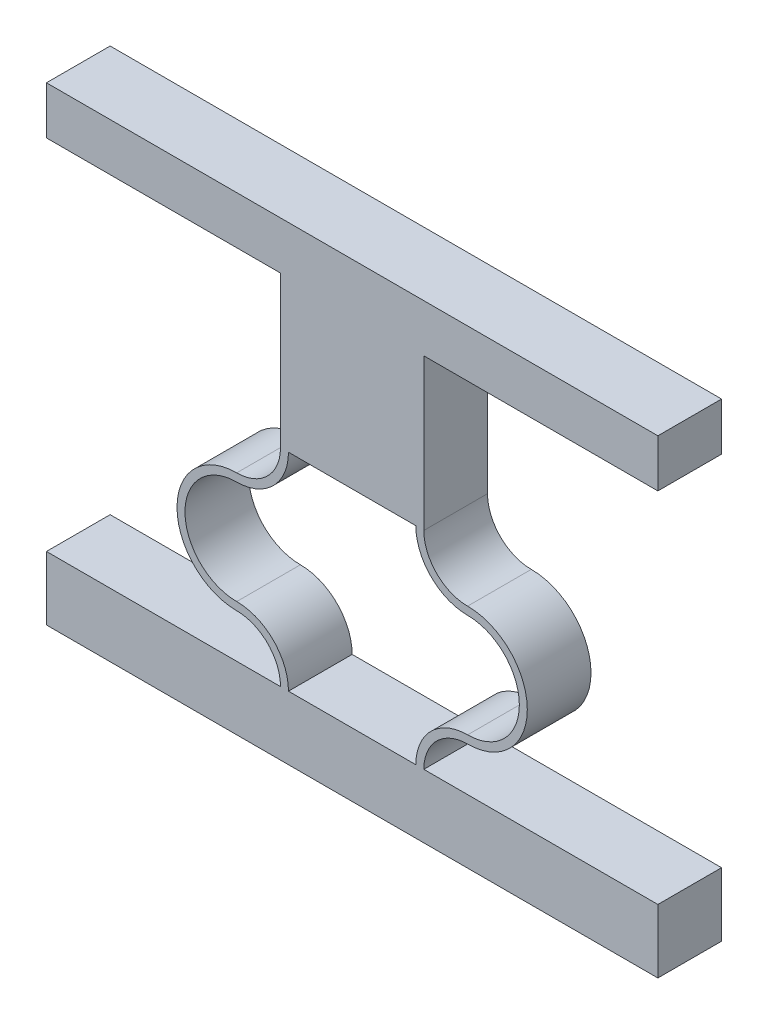
SolidWorks part; units mm, degrees
ref_plane "Front Plane" through (0, 0, 0) normal (0, 0, 1) x (1, 0, 0)
ref_plane "Top Plane" through (0, 0, 0) normal (0, 1, 0) x (1, 0, 0)
ref_plane "Right Plane" through (0, 0, 0) normal (1, 0, 0) x (0, 0, -1)
sketch "Sketch1" plane through (0, 0, 0) normal (0, 0, 1) x (1, 0, 0)
  line L4 (0, 11.5) -> (0, 0)
  line L5 (10.2, 0) -> (10.2, 13) construction
  line L6 (10.2, 13) -> (10.2, 15.9911) construction
  line L17 (9.7, 0) -> (0, 0)
  line L18 (10.7, 0) -> (20.4, 0)
  line L19 (20.4, 0) -> (20.4, 11.5)
  line L20 (10.7, 13.2411) -> (10.7, 14.4911)
  line L21 (9.7, 13.2411) -> (9.7, 14.4911)
  line L22 (10.7, 14.7411) -> (10.7, 15.9911)
  line L23 (10.7, 15.9911) -> (9.7, 15.9911)
  line L24 (9.7, 15.9911) -> (9.7, 14.7411)
  line L31 (-5, 13.25) -> (-5, -4)
  line L32 (-5, -4) -> (25.4, -4)
  line L33 (25.4, -4) -> (25.4, 13.25)
  line L34 (0, 11.75) -> (0, 13)
  line L36 (-5, 13.25) -> (0, 13.25)
  line L37 (25.4, 13.25) -> (20.4, 13.25)
  line L38 (20.4, 11.75) -> (20.4, 13)
  arc A0 (10.2, 13) -> (6.95, 9.75) centre (6.95, 13) cw
  arc A1 (6.95, 9.75) -> (6.95, 3.25) centre (6.95, 6.5) ccw
  arc A2 (6.95, 3.25) -> (10.2, 0) centre (6.95, 0) cw
  arc A3 (9.7, 12.9911) -> (6.95, 10.25) centre (6.95, 13) cw
  arc A4 (6.95, 10.25) -> (6.95, 2.75) centre (6.95, 6.5) ccw
  arc A5 (6.95, 2.75) -> (9.7, 0) centre (6.95, 0) cw
  arc A6 (9.7, 13) -> (6.95, 10.25) centre (6.95, 13) cw construction
  arc A7 (13.45, 3.25) -> (10.2, 0) centre (13.45, 0) ccw
  arc A8 (13.45, 2.75) -> (10.7, 0) centre (13.45, 0) ccw
  arc A9 (13.45, 9.75) -> (13.45, 3.25) centre (13.45, 6.5) cw
  arc A10 (13.45, 10.25) -> (13.45, 2.75) centre (13.45, 6.5) cw
  arc A11 (10.7, 12.9911) -> (13.45, 10.25) centre (13.45, 13) ccw
  arc A12 (10.2, 13) -> (13.45, 9.75) centre (13.45, 13) ccw
  spline S0 degree 4 poles (-2.0401, 11.8932) (-1.9772, 11.8846) (-1.8455, 11.8679) (-1.6624, 11.8447) (-1.3945, 11.8179) (-1.0936, 11.7897) (-0.7437, 11.7688) (-0.4752, 11.7554) (-0.0408, 11.749) (0.1102, 11.7499) (0.4738, 11.7558) (0.7092, 11.7679) (1.0334, 11.7851) (1.3516, 11.8128) (1.7502, 11.854) (2.1923, 11.9124) (2.7058, 11.9922) (3.3058, 12.1029) (4.0022, 12.2485) (4.9166, 12.4561) (5.9838, 12.707) (7.055, 12.9379) (8.1373, 13.1142) (9.0337, 13.2105) (9.8109, 13.2536) (10.5891, 13.2536) (11.3663, 13.2105) (12.2627, 13.1142) (13.3449, 12.9379) (14.4163, 12.707) (15.4832, 12.4561) (16.3198, 12.2662) (16.8578, 12.1523) (17.3629, 12.0533) (17.7764, 11.9798) (18.2035, 11.9124) (18.6563, 11.854) (18.9878, 11.8179) (19.2899, 11.793) (19.5137, 11.7765) (19.7423, 11.7659) (19.9174, 11.7558) (20.2941, 11.7499) (20.4363, 11.749) (20.8074, 11.7542) (21.0192, 11.7634) (21.2671, 11.7754) (21.4449, 11.7884) (21.6432, 11.8037) (21.8311, 11.8212) (22.0262, 11.8414) (22.2161, 11.864) (22.3445, 11.8804) (22.4082, 11.8889) (22.4399, 11.8932) knots 0 0 0 0 0 0.010394 0.020788 0.031182 0.041576 0.062112 0.07238 0.082649 0.098356 0.106209 0.114063 0.12977 0.145477 0.161184 0.176891 0.202819 0.228747 0.260161 0.291575 0.354403 0.405758 0.437172 0.468586 0.5 0.531414 0.562828 0.594242 0.645597 0.708425 0.739839 0.771253 0.784217 0.797181 0.823109 0.838816 0.854523 0.87023 0.878084 0.885937 0.893791 0.901644 0.917351 0.92762 0.937888 0.948156 0.958424 0.963621 0.968818 0.979212 0.989606 0.994803 1 1 1 1 1 construction
  spline S1 degree 4 poles (0, 11.75) (0.0812, 11.75) (0.1997, 11.7513) (0.4738, 11.7558) (0.7092, 11.7679) (1.0334, 11.7851) (1.3516, 11.8128) (1.7502, 11.854) (2.1923, 11.9124) (2.7058, 11.9922) (3.3058, 12.1029) (4.0022, 12.2485) (4.9166, 12.4561) (5.9838, 12.707) (7.055, 12.9379) (8.1373, 13.1142) (9.0337, 13.2105) (9.8109, 13.2536) (10.5891, 13.2536) (11.3663, 13.2105) (12.2627, 13.1142) (13.3449, 12.9379) (14.4163, 12.707) (15.4832, 12.4561) (16.3198, 12.2662) (16.8578, 12.1523) (17.3629, 12.0533) (17.7764, 11.9798) (18.2035, 11.9124) (18.6563, 11.854) (18.9878, 11.8179) (19.2899, 11.793) (19.5137, 11.7765) (19.7423, 11.7659) (19.9174, 11.7558) (20.2013, 11.7513) (20.3188, 11.75) (20.4, 11.75) knots 0.082649 0.082649 0.082649 0.082649 0.082649 0.098356 0.106209 0.114063 0.12977 0.145477 0.161184 0.176891 0.202819 0.228747 0.260161 0.291575 0.354403 0.405758 0.437172 0.468586 0.5 0.531414 0.562828 0.594242 0.645597 0.708425 0.739839 0.771253 0.784217 0.797181 0.823109 0.838816 0.854523 0.87023 0.878084 0.885937 0.893791 0.901644 0.917351 0.917351 0.917351 0.917351 0.917351
  spline S2 degree 4 poles (-2.0401, 13.1432) (-1.9772, 13.1346) (-1.8455, 13.1179) (-1.6624, 13.0947) (-1.3945, 13.0679) (-1.0936, 13.0397) (-0.7437, 13.0188) (-0.4752, 13.0054) (-0.0408, 12.999) (0.1102, 12.9999) (0.4738, 13.0058) (0.7092, 13.0179) (1.0334, 13.0351) (1.3516, 13.0628) (1.7502, 13.104) (2.1923, 13.1624) (2.7058, 13.2422) (3.3058, 13.3529) (4.0022, 13.4985) (4.9166, 13.7061) (5.9838, 13.957) (7.055, 14.1879) (8.1373, 14.3642) (9.0337, 14.4605) (9.8109, 14.5036) (10.5891, 14.5036) (11.3663, 14.4605) (12.2627, 14.3642) (13.3449, 14.1879) (14.4163, 13.957) (15.4832, 13.7061) (16.3198, 13.5162) (16.8578, 13.4023) (17.3629, 13.3033) (17.7764, 13.2298) (18.2035, 13.1624) (18.6563, 13.104) (18.9878, 13.0679) (19.2899, 13.043) (19.5137, 13.0265) (19.7423, 13.0159) (19.9174, 13.0058) (20.2941, 12.9999) (20.4363, 12.999) (20.8074, 13.0042) (21.0192, 13.0134) (21.2671, 13.0254) (21.4449, 13.0384) (21.6432, 13.0537) (21.8311, 13.0712) (22.0262, 13.0914) (22.2161, 13.114) (22.3445, 13.1304) (22.4082, 13.1389) (22.4399, 13.1432) knots 0 0 0 0 0 0.010394 0.020788 0.031182 0.041576 0.062112 0.07238 0.082649 0.098356 0.106209 0.114063 0.12977 0.145477 0.161184 0.176891 0.202819 0.228747 0.260161 0.291575 0.354403 0.405758 0.437172 0.468586 0.5 0.531414 0.562828 0.594242 0.645597 0.708425 0.739839 0.771253 0.784217 0.797181 0.823109 0.838816 0.854523 0.87023 0.878084 0.885937 0.893791 0.901644 0.917351 0.92762 0.937888 0.948156 0.958424 0.963621 0.968818 0.979212 0.989606 0.994803 1 1 1 1 1 construction
  spline S3 degree 4 poles (0, 13) (0.0812, 13) (0.1997, 13.0013) (0.4738, 13.0058) (0.7092, 13.0179) (1.0334, 13.0351) (1.3516, 13.0628) (1.7502, 13.104) (2.1923, 13.1624) (2.7058, 13.2422) (3.3058, 13.3529) (4.0022, 13.4985) (4.9166, 13.7061) (5.9838, 13.957) (7.055, 14.1879) (8.1373, 14.3642) (9.0337, 14.4605) (9.8109, 14.5036) (10.5891, 14.5036) (11.3663, 14.4605) (12.2627, 14.3642) (13.3449, 14.1879) (14.4163, 13.957) (15.4832, 13.7061) (16.3198, 13.5162) (16.8578, 13.4023) (17.3629, 13.3033) (17.7764, 13.2298) (18.2035, 13.1624) (18.6563, 13.104) (18.9878, 13.0679) (19.2899, 13.043) (19.5137, 13.0265) (19.7423, 13.0159) (19.9174, 13.0058) (20.2013, 13.0013) (20.3188, 13) (20.4, 13) knots 0.082649 0.082649 0.082649 0.082649 0.082649 0.098356 0.106209 0.114063 0.12977 0.145477 0.161184 0.176891 0.202819 0.228747 0.260161 0.291575 0.354403 0.405758 0.437172 0.468586 0.5 0.531414 0.562828 0.594242 0.645597 0.708425 0.739839 0.771253 0.784217 0.797181 0.823109 0.838816 0.854523 0.87023 0.878084 0.885937 0.893791 0.901644 0.917351 0.917351 0.917351 0.917351 0.917351
  spline S4 degree 4 poles (-2.0401, 13.3932) (-1.9772, 13.3846) (-1.8455, 13.3679) (-1.6624, 13.3447) (-1.3945, 13.3179) (-1.0936, 13.2897) (-0.7437, 13.2688) (-0.4752, 13.2554) (-0.0408, 13.249) (0.1102, 13.2499) (0.4738, 13.2558) (0.7092, 13.2679) (1.0334, 13.2851) (1.3516, 13.3128) (1.7502, 13.354) (2.1923, 13.4124) (2.7058, 13.4922) (3.3058, 13.6029) (4.0022, 13.7485) (4.9166, 13.9561) (5.9838, 14.207) (7.055, 14.4379) (8.1373, 14.6142) (9.0337, 14.7105) (9.8109, 14.7536) (10.5891, 14.7536) (11.3663, 14.7105) (12.2627, 14.6142) (13.3449, 14.4379) (14.4163, 14.207) (15.4832, 13.9561) (16.3198, 13.7662) (16.8578, 13.6523) (17.3629, 13.5533) (17.7764, 13.4798) (18.2035, 13.4124) (18.6563, 13.354) (18.9878, 13.3179) (19.2899, 13.293) (19.5137, 13.2765) (19.7423, 13.2659) (19.9174, 13.2558) (20.2941, 13.2499) (20.4363, 13.249) (20.8074, 13.2542) (21.0192, 13.2634) (21.2671, 13.2754) (21.4449, 13.2884) (21.6432, 13.3037) (21.8311, 13.3212) (22.0262, 13.3414) (22.2161, 13.364) (22.3445, 13.3804) (22.4082, 13.3889) (22.4399, 13.3932) knots 0 0 0 0 0 0.010394 0.020788 0.031182 0.041576 0.062112 0.07238 0.082649 0.098356 0.106209 0.114063 0.12977 0.145477 0.161184 0.176891 0.202819 0.228747 0.260161 0.291575 0.354403 0.405758 0.437172 0.468586 0.5 0.531414 0.562828 0.594242 0.645597 0.708425 0.739839 0.771253 0.784217 0.797181 0.823109 0.838816 0.854523 0.87023 0.878084 0.885937 0.893791 0.901644 0.917351 0.92762 0.937888 0.948156 0.958424 0.963621 0.968818 0.979212 0.989606 0.994803 1 1 1 1 1 construction
  spline S5 degree 4 poles (0, 13.25) (0.0812, 13.25) (0.1997, 13.2513) (0.4738, 13.2558) (0.7092, 13.2679) (1.0334, 13.2851) (1.3516, 13.3128) (1.7502, 13.354) (2.1923, 13.4124) (2.7058, 13.4922) (3.3058, 13.6029) (4.0022, 13.7485) (4.9166, 13.9561) (5.9838, 14.207) (7.055, 14.4379) (8.1373, 14.6142) (9.0337, 14.7105) (9.8109, 14.7536) (10.5891, 14.7536) (11.3663, 14.7105) (12.2627, 14.6142) (13.3449, 14.4379) (14.4163, 14.207) (15.4832, 13.9561) (16.3198, 13.7662) (16.8578, 13.6523) (17.3629, 13.5533) (17.7764, 13.4798) (18.2035, 13.4124) (18.6563, 13.354) (18.9878, 13.3179) (19.2899, 13.293) (19.5137, 13.2765) (19.7423, 13.2659) (19.9174, 13.2558) (20.2013, 13.2513) (20.3188, 13.25) (20.4, 13.25) knots 0.082649 0.082649 0.082649 0.082649 0.082649 0.098356 0.106209 0.114063 0.12977 0.145477 0.161184 0.176891 0.202819 0.228747 0.260161 0.291575 0.354403 0.405758 0.437172 0.468586 0.5 0.531414 0.562828 0.594242 0.645597 0.708425 0.739839 0.771253 0.784217 0.797181 0.823109 0.838816 0.854523 0.87023 0.878084 0.885937 0.893791 0.901644 0.917351 0.917351 0.917351 0.917351 0.917351
  spline S8 degree 4 poles (-2.0401, 11.6432) (-1.9772, 11.6346) (-1.8455, 11.6179) (-1.6624, 11.5947) (-1.3945, 11.5679) (-1.0936, 11.5397) (-0.7437, 11.5188) (-0.4752, 11.5054) (-0.0408, 11.499) (0.1102, 11.4999) (0.4738, 11.5058) (0.7092, 11.5179) (1.0334, 11.5351) (1.3516, 11.5628) (1.7502, 11.604) (2.1923, 11.6624) (2.7058, 11.7422) (3.3058, 11.8529) (4.0022, 11.9985) (4.9166, 12.2061) (5.9838, 12.457) (7.055, 12.6879) (8.1373, 12.8642) (9.0337, 12.9605) (9.8109, 13.0036) (10.5891, 13.0036) (11.3663, 12.9605) (12.2627, 12.8642) (13.3449, 12.6879) (14.4163, 12.457) (15.4832, 12.2061) (16.3198, 12.0162) (16.8578, 11.9023) (17.3629, 11.8033) (17.7764, 11.7298) (18.2035, 11.6624) (18.6563, 11.604) (18.9878, 11.5679) (19.2899, 11.543) (19.5137, 11.5265) (19.7423, 11.5159) (19.9174, 11.5058) (20.2941, 11.4999) (20.4363, 11.499) (20.8074, 11.5042) (21.0192, 11.5134) (21.2671, 11.5254) (21.4449, 11.5384) (21.6432, 11.5537) (21.8311, 11.5712) (22.0262, 11.5914) (22.2161, 11.614) (22.3445, 11.6304) (22.4082, 11.6389) (22.4399, 11.6432) knots 0 0 0 0 0 0.010394 0.020788 0.031182 0.041576 0.062112 0.07238 0.082649 0.098356 0.106209 0.114063 0.12977 0.145477 0.161184 0.176891 0.202819 0.228747 0.260161 0.291575 0.354403 0.405758 0.437172 0.468586 0.5 0.531414 0.562828 0.594242 0.645597 0.708425 0.739839 0.771253 0.784217 0.797181 0.823109 0.838816 0.854523 0.87023 0.878084 0.885937 0.893791 0.901644 0.917351 0.92762 0.937888 0.948156 0.958424 0.963621 0.968818 0.979212 0.989606 0.994803 1 1 1 1 1 construction
  spline S9 degree 4 poles (0, 11.5) (0.0812, 11.5) (0.1997, 11.5013) (0.4738, 11.5058) (0.7092, 11.5179) (1.0334, 11.5351) (1.3516, 11.5628) (1.7502, 11.604) (2.1923, 11.6624) (2.7058, 11.7422) (3.3058, 11.8529) (4.0022, 11.9985) (4.9166, 12.2061) (5.9838, 12.457) (7.055, 12.6879) (8.1373, 12.8642) (9.0337, 12.9605) (9.8109, 13.0036) (10.5891, 13.0036) (11.3663, 12.9605) (12.2627, 12.8642) (13.3449, 12.6879) (14.4163, 12.457) (15.4832, 12.2061) (16.3198, 12.0162) (16.8578, 11.9023) (17.3629, 11.8033) (17.7764, 11.7298) (18.2035, 11.6624) (18.6563, 11.604) (18.9878, 11.5679) (19.2899, 11.543) (19.5137, 11.5265) (19.7423, 11.5159) (19.9174, 11.5058) (20.2013, 11.5013) (20.3188, 11.5) (20.4, 11.5) knots 0.082649 0.082649 0.082649 0.082649 0.082649 0.098356 0.106209 0.114063 0.12977 0.145477 0.161184 0.176891 0.202819 0.228747 0.260161 0.291575 0.354403 0.405758 0.437172 0.468586 0.5 0.531414 0.562828 0.594242 0.645597 0.708425 0.739839 0.771253 0.784217 0.797181 0.823109 0.838816 0.854523 0.87023 0.878084 0.885937 0.893791 0.901644 0.917351 0.917351 0.917351 0.917351 0.917351
  dimension "D4" = 0.25
  dimension "D6" = 4
  dimension "D1" = 13
  dimension "D2" = 0.5
  dimension "D3" = 0.25
  dimension "D7" = 5
  dimension "D5" = 1.5
extrude "Boss-Extrude1" add sketch "Sketch1" along normal blind 4
sketch "Sketch4" plane through (0, 15.9911, 0) normal (0, 1, 0) x (1, 0, 0)
  line L24 (10.7, 0) -> (9.7, 0)
  line L25 (9.7, 0) -> (9.7, -4)
  line L26 (10.7, 0) -> (9.7, 0)
  line L27 (10.7, -4) -> (10.7, 0)
  line L29 (9.7, 0) -> (9.7, -4)
  line L31 (10.7, -4) -> (10.7, 0)
  line L32 (9.7, -4) -> (10.7, -4)
  line L33 (9.7, -4) -> (10.7, -4)
  dimension "D1" = 0
extrude "Boss-Extrude2" add sketch "Sketch4" along normal blind 1.5
mirror "Mirror3" [suppressed]
ref_plane "Plane1" through (10.2, 0, 0) normal (-1, 0, 0) x (0, 0, 1)
split "Split2" trim tools "Plane1" bodies to split 179 102 resulting bodies 225
sketch "Sketch7" plane through (10.2, 0, 0) normal (-1, 0, 0) x (0, 0, 1)
  line L4 (0, 13) -> (4, 13)
  line L12 (0, 13) -> (4, 13)
  line L13 (0, 13) -> (4, 13)
  line L14 (4, 13) -> (4, 17.4911)
  line L15 (4, 13) -> (4, 17.4911)
  line L20 (4, 0) -> (0, 0)
  line L22 (4, 0) -> (0, 0)
  line L23 (0, -4) -> (4, -4)
  line L27 (0, -4) -> (4, -4)
  line L31 (4, 17.4911) -> (0, 17.4911)
  line L33 (0, 17.4911) -> (0, 13)
  line L34 (0, 17.4911) -> (0, 13)
  line L36 (4, -4) -> (4, 0)
  line L38 (0, 13) -> (4, 13)
  line L39 (0, 13) -> (4, 13)
  line L40 (4, 13) -> (4, 17.4911)
  line L41 (4, 13) -> (4, 17.4911)
  line L51 (4, 17.4911) -> (0, 17.4911)
  line L52 (4, 17.4911) -> (0, 17.4911)
  line L53 (0, 17.4911) -> (0, 13)
  line L54 (0, 17.4911) -> (0, 13)
  line L55 (0, 13) -> (4, 13)
  line L59 (4, -4) -> (4, 0)
  line L60 (0, 0) -> (0, -4)
  line L61 (0, 0) -> (0, -4)
  line L62 (4, 13) -> (4, 17.4911)
  line L64 (4, 13) -> (4, 17.4911)
  line L66 (4, 17.4911) -> (0, 17.4911)
  line L67 (4, 17.4911) -> (0, 17.4911)
  line L68 (0, 17.4911) -> (0, 13)
  line L69 (0, 17.4911) -> (0, 13)
  line L70 (4, 17.4911) -> (0, 17.4911)
  dimension "D1" = 0
  dimension "D2" = 0
  dimension "D3" = 0
  dimension "D4" = 0
extrude "Boss-Extrude3" add sketch "Sketch7" along normal blind 4
mirror "Mirror2" about plane through (6.2, 0, 0) normal (-1, 0, 0) of bodies 226
other "Move Face1" face at (6.2, 17.4911, 2) parameters "D1"=5
sketch "Sketch8" plane through (0, 0, 4) normal (0, 0, 1) x (1, 0, 0)
  line L1 (-13, 25.4911) -> (25.4, 25.4911)
  line L2 (-13, 25.4911) -> (-13, 22.4911)
  line L3 (-13, 22.4911) -> (25.4, 22.4911)
  line L4 (25.4, 25.4911) -> (25.4, 22.4911)
  line L5 (25.4, -4) -> (25.4, 13.25) construction
  line L6 (-13, -4) -> (-13, 13.25) construction
  dimension "D1" = 3
extrude "Boss-Extrude4" add sketch "Sketch8" against normal up to surface (4 mm away) up to face at (6.2, 12.0956, 0)
sketch "Sketch10" plane through (0, 0, 4) normal (0, 0, 1) x (1, 0, 0)
  line L0 (10.7, 12.9911) -> (10.7, 13.2411)
  line L1 (10.7, 13.2411) -> (10.7, 14.4911)
  line L2 (10.7, 14.4911) -> (10.7, 14.7411)
  line L3 (10.7, 14.7411) -> (20.4, 14.7411)
  line L4 (20.4, 14.7411) -> (20.4, 11.5)
  line L5 (20.4, 11.5) -> (15.4354, 11.5)
  line L6 (15.4354, 11.5) -> (10.7, 12.9911)
  line L7 (20.4, 0) -> (20.4, 11.5) construction
  line L8 (1.7, 14.4911) -> (1.7, 14.7411)
  line L9 (1.7, 12.9911) -> (1.7, 13.2411)
  line L10 (-8, 11.5) -> (-8, 11.75)
  line L11 (-8, 13) -> (-8, 13.25)
  spline S0 degree 4 poles (-28.5008, 3012.671) (11.0034, -84.0572) (30.5418, -2.215) (14.7236, 14.4315) (0.1373, 12.8642) (-0.9449, 12.6879) (-2.0163, 12.457) (-3.0832, 12.2061) (-3.9198, 12.0162) (-4.4578, 11.9023) (-4.9629, 11.8033) (-5.3764, 11.7298) (-5.8035, 11.6624) (-6.2563, 11.604) (-6.5878, 11.5679) (-6.8899, 11.543) (-7.1137, 11.5265) (-7.3423, 11.5159) (-8.4137, 11.4545) (-17.3216, 11.5889) (119.3564, 11.9225) (-3006.9885, 12.1726) knots -1.723324 -1.723324 -1.723324 -1.723324 -1.723324 0.531414 0.562828 0.594242 0.645597 0.708425 0.739839 0.771253 0.784217 0.797181 0.823109 0.838816 0.854523 0.87023 0.878084 0.885937 0.893791 0.901644 1.118355 1.118355 1.118355 1.118355 1.118355 only from (1.7, 12.9911) to (-8, 11.5) construction
  spline S1 degree 4 poles (-28.5008, 3012.921) (11.0034, -83.8072) (30.5418, -1.965) (14.7236, 14.6815) (0.1373, 13.1142) (-0.9449, 12.9379) (-2.0163, 12.707) (-3.0832, 12.4561) (-3.9198, 12.2662) (-4.4578, 12.1523) (-4.9629, 12.0533) (-5.3764, 11.9798) (-5.8035, 11.9124) (-6.2563, 11.854) (-6.5878, 11.8179) (-6.8899, 11.793) (-7.1137, 11.7765) (-7.3423, 11.7659) (-8.4137, 11.7045) (-17.3216, 11.8389) (119.3564, 12.1725) (-3006.9885, 12.4226) knots -1.723324 -1.723324 -1.723324 -1.723324 -1.723324 0.531414 0.562828 0.594242 0.645597 0.708425 0.739839 0.771253 0.784217 0.797181 0.823109 0.838816 0.854523 0.87023 0.878084 0.885937 0.893791 0.901644 1.118355 1.118355 1.118355 1.118355 1.118355 only from (1.7, 13.2411) to (-8, 11.75) construction
  spline S2 degree 4 poles (-28.5008, 3014.171) (11.0034, -82.5572) (30.5418, -0.715) (14.7236, 15.9315) (0.1373, 14.3642) (-0.9449, 14.1879) (-2.0163, 13.957) (-3.0832, 13.7061) (-3.9198, 13.5162) (-4.4578, 13.4023) (-4.9629, 13.3033) (-5.3764, 13.2298) (-5.8035, 13.1624) (-6.2563, 13.104) (-6.5878, 13.0679) (-6.8899, 13.043) (-7.1137, 13.0265) (-7.3423, 13.0159) (-8.4137, 12.9545) (-17.3216, 13.0889) (119.3564, 13.4225) (-3006.9885, 13.6726) knots -1.723324 -1.723324 -1.723324 -1.723324 -1.723324 0.531414 0.562828 0.594242 0.645597 0.708425 0.739839 0.771253 0.784217 0.797181 0.823109 0.838816 0.854523 0.87023 0.878084 0.885937 0.893791 0.901644 1.118355 1.118355 1.118355 1.118355 1.118355 only from (1.7, 14.4911) to (-8, 13) construction
  spline S3 degree 4 poles (-28.5008, 3014.421) (11.0034, -82.3072) (30.5418, -0.465) (14.7236, 16.1815) (0.1373, 14.6142) (-0.9449, 14.4379) (-2.0163, 14.207) (-3.0832, 13.9561) (-3.9198, 13.7662) (-4.4578, 13.6523) (-4.9629, 13.5533) (-5.3764, 13.4798) (-5.8035, 13.4124) (-6.2563, 13.354) (-6.5878, 13.3179) (-6.8899, 13.293) (-7.1137, 13.2765) (-7.3423, 13.2659) (-8.4137, 13.2045) (-17.3216, 13.3389) (119.3564, 13.6725) (-3006.9885, 13.9226) knots -1.723324 -1.723324 -1.723324 -1.723324 -1.723324 0.531414 0.562828 0.594242 0.645597 0.708425 0.739839 0.771253 0.784217 0.797181 0.823109 0.838816 0.854523 0.87023 0.878084 0.885937 0.893791 0.901644 1.118355 1.118355 1.118355 1.118355 1.118355 only from (1.7, 14.7411) to (-8, 13.25) construction
  spline S4 degree 4 poles (1.7, 12.9911) (1.6306, 12.9887) (1.3669, 12.9776) (0.9094, 12.9472) (0.1373, 12.8642) (-0.9449, 12.6879) (-2.0163, 12.457) (-3.0832, 12.2061) (-3.9198, 12.0162) (-4.4578, 11.9023) (-4.9629, 11.8033) (-5.3764, 11.7298) (-5.8035, 11.6624) (-6.2563, 11.604) (-6.5878, 11.5679) (-6.8899, 11.543) (-7.1137, 11.5265) (-7.3423, 11.5159) (-7.5174, 11.5058) (-7.8013, 11.5013) (-7.9188, 11.5) (-8, 11.5) knots 0.520197 0.520197 0.520197 0.520197 0.520197 0.531414 0.562828 0.594242 0.645597 0.708425 0.739839 0.771253 0.784217 0.797181 0.823109 0.838816 0.854523 0.87023 0.878084 0.885937 0.893791 0.901644 0.917351 0.917351 0.917351 0.917351 0.917351
  spline S5 degree 4 poles (1.7, 13.2411) (1.6306, 13.2387) (1.3669, 13.2276) (0.9094, 13.1972) (0.1373, 13.1142) (-0.9449, 12.9379) (-2.0163, 12.707) (-3.0832, 12.4561) (-3.9198, 12.2662) (-4.4578, 12.1523) (-4.9629, 12.0533) (-5.3764, 11.9798) (-5.8035, 11.9124) (-6.2563, 11.854) (-6.5878, 11.8179) (-6.8899, 11.793) (-7.1137, 11.7765) (-7.3423, 11.7659) (-7.5174, 11.7558) (-7.8013, 11.7513) (-7.9188, 11.75) (-8, 11.75) knots 0.520197 0.520197 0.520197 0.520197 0.520197 0.531414 0.562828 0.594242 0.645597 0.708425 0.739839 0.771253 0.784217 0.797181 0.823109 0.838816 0.854523 0.87023 0.878084 0.885937 0.893791 0.901644 0.917351 0.917351 0.917351 0.917351 0.917351
  spline S6 degree 4 poles (1.7, 14.4911) (1.6306, 14.4887) (1.3669, 14.4776) (0.9094, 14.4472) (0.1373, 14.3642) (-0.9449, 14.1879) (-2.0163, 13.957) (-3.0832, 13.7061) (-3.9198, 13.5162) (-4.4578, 13.4023) (-4.9629, 13.3033) (-5.3764, 13.2298) (-5.8035, 13.1624) (-6.2563, 13.104) (-6.5878, 13.0679) (-6.8899, 13.043) (-7.1137, 13.0265) (-7.3423, 13.0159) (-7.5174, 13.0058) (-7.8013, 13.0013) (-7.9188, 13) (-8, 13) knots 0.520197 0.520197 0.520197 0.520197 0.520197 0.531414 0.562828 0.594242 0.645597 0.708425 0.739839 0.771253 0.784217 0.797181 0.823109 0.838816 0.854523 0.87023 0.878084 0.885937 0.893791 0.901644 0.917351 0.917351 0.917351 0.917351 0.917351
  spline S7 degree 4 poles (1.7, 14.7411) (1.6306, 14.7387) (1.3669, 14.7276) (0.9094, 14.6972) (0.1373, 14.6142) (-0.9449, 14.4379) (-2.0163, 14.207) (-3.0832, 13.9561) (-3.9198, 13.7662) (-4.4578, 13.6523) (-4.9629, 13.5533) (-5.3764, 13.4798) (-5.8035, 13.4124) (-6.2563, 13.354) (-6.5878, 13.3179) (-6.8899, 13.293) (-7.1137, 13.2765) (-7.3423, 13.2659) (-7.5174, 13.2558) (-7.8013, 13.2513) (-7.9188, 13.25) (-8, 13.25) knots 0.520197 0.520197 0.520197 0.520197 0.520197 0.531414 0.562828 0.594242 0.645597 0.708425 0.739839 0.771253 0.784217 0.797181 0.823109 0.838816 0.854523 0.87023 0.878084 0.885937 0.893791 0.901644 0.917351 0.917351 0.917351 0.917351 0.917351
extrude "Cut-Extrude1" cut sketch "Sketch10" against normal through all
sketch "Sketch11" plane through (0, 0, 4) normal (0, 0, 1) x (1, 0, 0)
  line L0 (25.4, -4) -> (25.4, 13.25) construction
  line L1 (-13, 13.25) -> (-8, 13.25)
  line L2 (-13, 13.25) -> (-13, 0)
  line L3 (-13, 0) -> (-8, 0)
  line L4 (-8, 13.25) -> (-8, 0)
  line L5 (20.4, 13.25) -> (25.4, 13.25)
  line L6 (20.4, 13.25) -> (20.4, 0)
  line L7 (20.4, 0) -> (25.4, 0)
  line L8 (25.4, 13.25) -> (25.4, 0)
  line L9 (10.7, 0) -> (20.4, 0) construction
extrude "Cut-Extrude2" cut sketch "Sketch11" against normal through all
